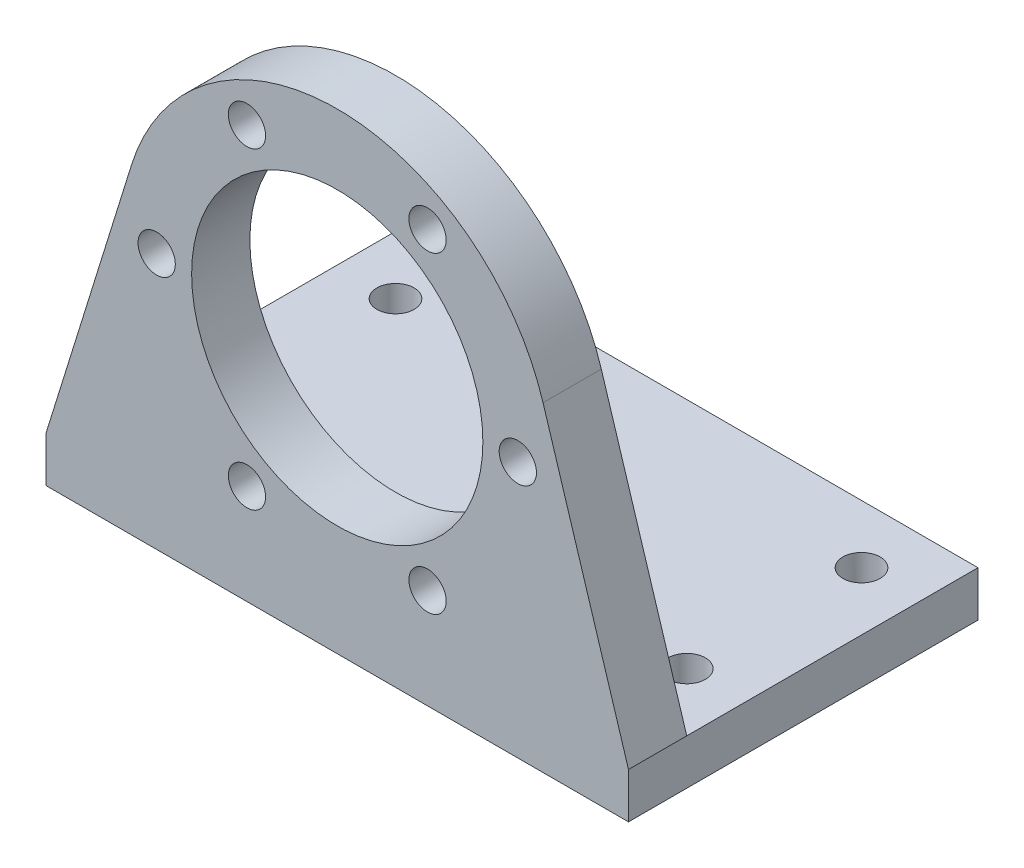
SolidWorks part; units mm, degrees
ref_plane "前视基准面" through (0, 0, 0) normal (0, 0, 1) x (1, 0, 0)
ref_plane "上视基准面" through (0, 0, 0) normal (0, 1, 0) x (1, 0, 0)
ref_plane "右视基准面" through (0, 0, 0) normal (1, 0, 0) x (0, 0, -1)
sketch "草图1" plane through (0, 0, 0) normal (0, 0, 1) x (1, 0, 0)
  line L0 (-25, -22) -> (25, -22)
  line L1 (0, 0) -> (0, -22) construction
  line L2 (-25, -22) -> (-25, -18.1033)
  line L3 (-25, -18.1033) -> (-17.6663, 5.4911)
  line L4 (25, -22) -> (25, -18.1033)
  line L5 (25, -18.1033) -> (17.6663, 5.4911)
  circle A1 centre (-15.5, 0) radius 1.6
  circle A2 centre (-7.75, 13.4234) radius 1.6
  circle A3 centre (7.75, 13.4234) radius 1.6
  circle A4 centre (15.5, 0) radius 1.6
  circle A5 centre (7.75, -13.4234) radius 1.6
  circle A6 centre (-7.75, -13.4234) radius 1.6
  arc A7 (17.6663, 5.4911) -> (-17.6663, 5.4911) centre (0, 0) ccw
  circle A8 centre (0, 0) radius 12.5
  point P17 (0, 0)
  dimension "D1" = 6
  dimension "D2" = 25
  dimension "D3" = 37
  dimension "D4" = 22
  dimension "D5" = 25
extrude "凸台-拉伸1" add sketch "草图1" along normal blind 5
sketch "草图2" plane through (0, 0, 0) normal (0, 0, -1) x (-1, 0, 0)
  line L0 (-25, -22) -> (-25, -18.1033)
  line L1 (-25, -18.1033) -> (25, -18.1033)
  line L2 (25, -18.1033) -> (25, -22)
  line L3 (25, -22) -> (-25, -22)
extrude "凸台-拉伸2" add sketch "草图2" along normal blind 25
sketch "草图3" plane through (0, -18.1033, 0) normal (0, 1, 0) x (1, 0, 0)
  line L0 (0, 25) -> (0, 0) construction
  line L1 (-25, 25) -> (25, 25) construction
  line L2 (-25, 12.5) -> (25, 12.5) construction
  line L3 (-25, 25) -> (-25, 0) construction
  line L4 (25, 25) -> (25, 0) construction
  circle A0 centre (-20, 20) radius 1.6
  circle A1 centre (20, 20) radius 1.6
  circle A2 centre (20, 5) radius 1.6
  circle A3 centre (-20, 5) radius 1.6
  dimension "D1" = 20
  dimension "D2" = 5
extrude "切除-拉伸1" cut sketch "草图3" against normal blind 25
